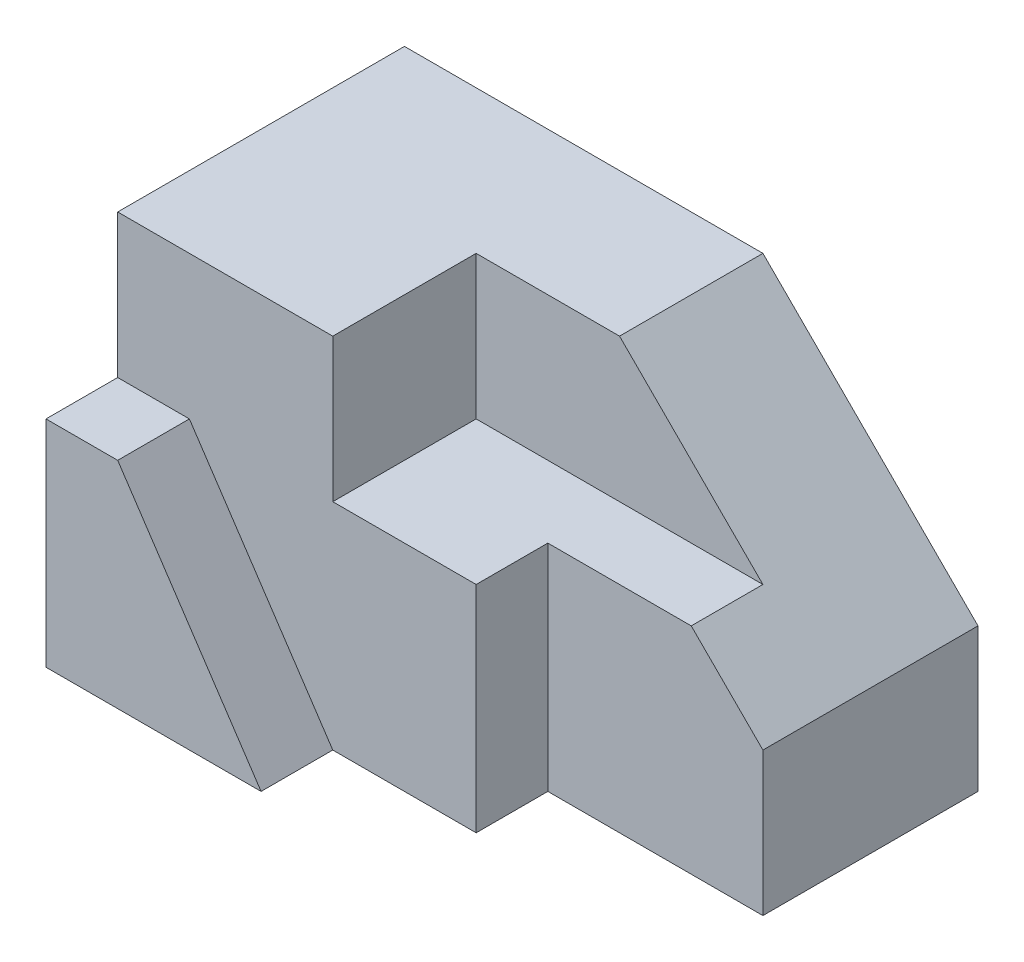
SolidWorks part; units mm, degrees
ref_plane "Front Plane" through (0, 0, 0) normal (0, 0, 1) x (1, 0, 0)
ref_plane "Top Plane" through (0, 0, 0) normal (0, 1, 0) x (1, 0, 0)
ref_plane "Right Plane" through (0, 0, 0) normal (1, 0, 0) x (0, 0, -1)
sketch "Sketch1" plane through (0, 0, 0) normal (0, 0, 1) x (1, 0, 0)
  line L1 (0, 0) -> (80, 0)
  line L2 (0, 0) -> (0, 50)
  line L3 (0, 50) -> (80, 50)
  line L4 (80, 0) -> (80, 50)
  dimension "D1" = 80
  dimension "D2" = 50
extrude "Boss-Extrude1" add sketch "Sketch1" against normal blind 50
sketch "Sketch2" plane through (0, 0, 0) normal (0, 0, 1) x (1, 0, 0)
  line L0 (0, 30) -> (0, 50)
  line L1 (0, 50) -> (0, 0) construction
  line L2 (0, 50) -> (80, 50)
  line L3 (80, 50) -> (80, 0)
  line L4 (80, 0) -> (30, 0)
  line L5 (0, 0) -> (80, 0) construction
  line L6 (30, 0) -> (10, 30)
  line L7 (10, 30) -> (0, 30)
  dimension "D1" = 10
  dimension "D2" = 20
  dimension "D3" = 30
extrude "Cut-Extrude1" cut sketch "Sketch2" against normal blind 10
sketch "Sketch3" plane through (0, 0, -10) normal (0, 0, 1) x (1, 0, 0)
  line L0 (50, 50) -> (80, 20)
  line L1 (80, 50) -> (0, 50) construction
  line L2 (80, 0) -> (80, 50) construction
  line L3 (80, 20) -> (80, 50)
  line L4 (80, 50) -> (50, 50)
  dimension "D1" = 30
  dimension "D2" = 30
extrude "Cut-Extrude2" cut sketch "Sketch3" against normal blind 56
sketch "Sketch4" plane through (0, 0, 0) normal (0, -1, 0) x (1, 0, 0)
  line L1 (80, -10) -> (50, -10)
  line L2 (80, -10) -> (80, -20)
  line L3 (80, -20) -> (50, -20)
  line L4 (50, -10) -> (50, -20)
  dimension "D1" = 10
  dimension "D2" = 30
extrude "Cut-Extrude3" cut sketch "Sketch4" against normal blind 56
sketch "Sketch5" plane through (0, 50, 0) normal (0, 1, 0) x (1, 0, 0)
  line L0 (0, 50) -> (0, 10) construction
  line L1 (30, 30) -> (112.1412, 30)
  line L2 (30, 30) -> (30, 10)
  line L3 (30, 10) -> (112.1412, 10)
  line L4 (112.1412, 30) -> (112.1412, 10)
  line L5 (50, 10) -> (0, 10) construction
  dimension "D1" = 30
  dimension "D2" = 20
  dimension "D3" = 0
  dimension "D4" = 82.1412
extrude "Cut-Extrude4" cut sketch "Sketch5" against normal blind 20
